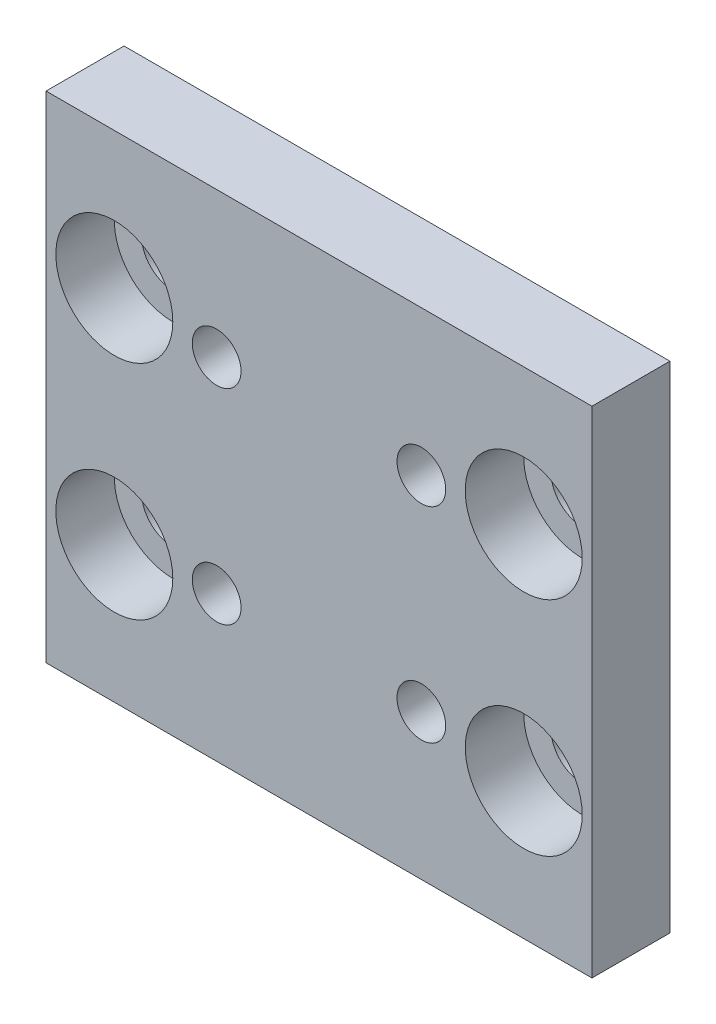
SolidWorks part; units mm, degrees
ref_plane "Front Plane" through (0, 0, 0) normal (0, 0, 1) x (1, 0, 0)
ref_plane "Top Plane" through (0, 0, 0) normal (0, 1, 0) x (1, 0, 0)
ref_plane "Right Plane" through (0, 0, 0) normal (1, 0, 0) x (0, 0, -1)
sketch "Sketch1" plane through (0, 0, 0) normal (0, 0, 1) x (1, 0, 0)
  line L0 (0, 12.7) -> (28, 12.7) construction
  line L1 (0, 0) -> (28, 0)
  line L2 (0, 0) -> (0, 25.4)
  line L3 (0, 25.4) -> (28, 25.4)
  line L4 (28, 0) -> (28, 25.4)
  line L5 (14, 0) -> (14, 25.4) construction
  circle A0 centre (8.75, 17.95) radius 1.25
  circle A1 centre (19.25, 17.95) radius 1.25
  circle A2 centre (19.25, 7.45) radius 1.25
  circle A3 centre (8.75, 7.45) radius 1.25
  circle A4 centre (3.5, 18.4) radius 1.6
  circle A5 centre (3.5, 7) radius 1.6
  circle A6 centre (24.5, 7) radius 1.6
  circle A7 centre (24.5, 18.4) radius 1.6
  dimension "D3" = 10.5
  dimension "D4" = 2.5
  dimension "D5" = 2.5
  dimension "D6" = 2.5
  dimension "D7" = 2.5
  dimension "D9" = 10.5
  dimension "D10" = 10.5
  dimension "D11" = 5.25
  dimension "D12" = 5.25
  dimension "D13" = 5.25
  dimension "D14" = 5.25
  dimension "D15" = 3.2
  dimension "D16" = 3.2
  dimension "D17" = 3.2
  dimension "D18" = 3.2
  dimension "D19" = 10.5
  dimension "D20" = 10.5
  dimension "D21" = 10.5
  dimension "D22" = 10.5
  dimension "D23" = 5.7
  dimension "D24" = 5.7
  dimension "D25" = 5.7
  dimension "D26" = 5.7
  dimension "D1" = 28
  dimension "D2" = 25.4
  dimension "10,5" = 10.5
extrude "Boss-Extrude1" add sketch "Sketch1" along normal blind 4
cosmetic thread "Cosmetic Thread1" parameters "D2"=3
cosmetic thread "Cosmetic Thread2" parameters "D2"=3
cosmetic thread "Cosmetic Thread3" parameters "D2"=3
cosmetic thread "Cosmetic Thread4" parameters "D2"=3
sketch "Sketch2" plane through (0, 0, 4) normal (0, 0, 1) x (1, 0, 0)
  circle A0 centre (24.5, 18.4) radius 3
  circle A1 centre (3.5, 18.4) radius 3
  circle A2 centre (3.5, 7) radius 3
  circle A3 centre (24.5, 7) radius 3
  dimension "D1" = 6
  dimension "D2" = 6
  dimension "D3" = 6
  dimension "D4" = 6
extrude "Cut-Extrude1" cut sketch "Sketch2" against normal blind 3
